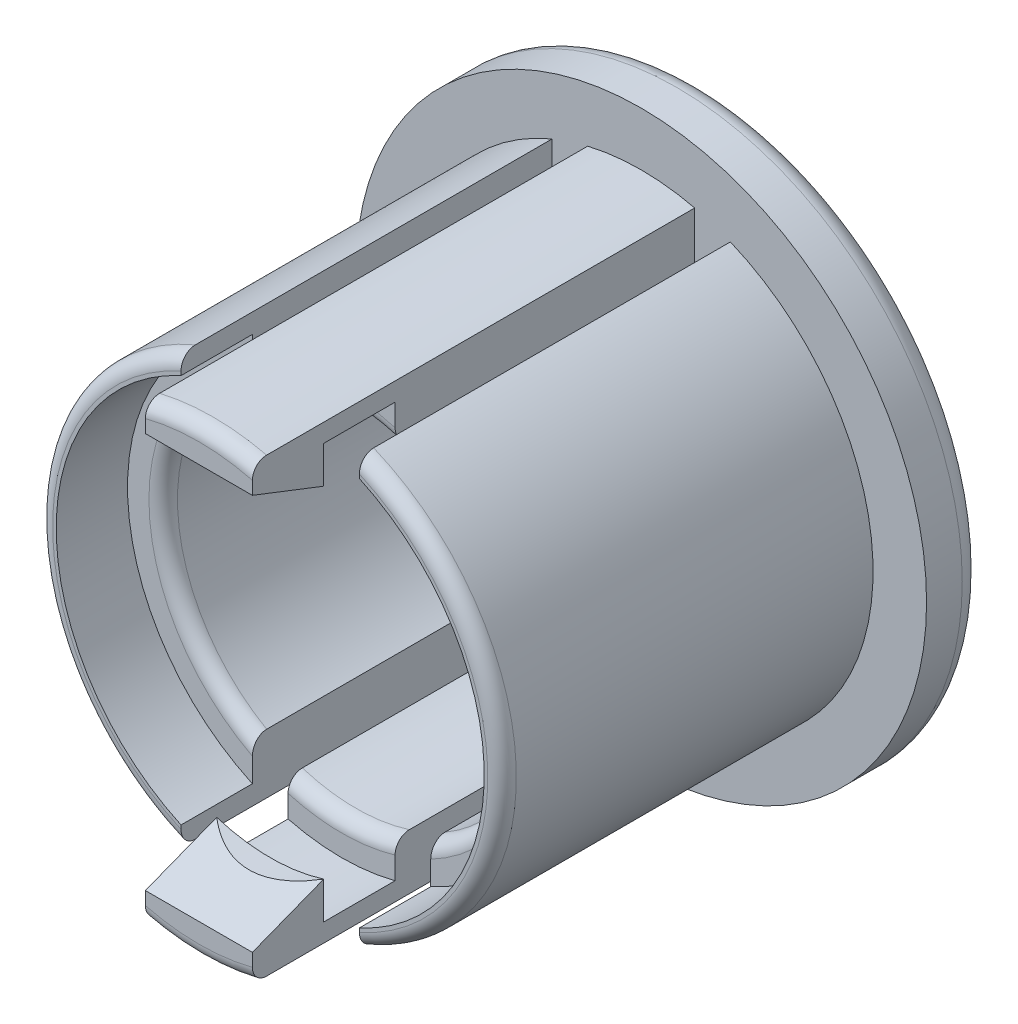
SolidWorks part; units mm, degrees
material "ABS"
ref_plane "Спереди" through (0, 0, 0) normal (0, 0, 1) x (1, 0, 0)
ref_plane "Сверху" through (0, 0, 0) normal (0, 1, 0) x (1, 0, 0)
ref_plane "Справа" through (0, 0, 0) normal (1, 0, 0) x (0, 0, -1)
sketch "Эскиз1" plane through (0, 0, 0) normal (0, 0, 1) x (1, 0, 0)
  circle A0 centre (0, 0) radius 4
  dimension "D1" = 8
extrude "Бобышка-Вытянуть1" add sketch "Эскиз1" along normal blind 0.8
sketch "Эскиз2" plane through (0, 0, 0.8) normal (0, 0, 1) x (1, 0, 0)
  circle A0 centre (0, 0) radius 3.25
  dimension "D1" = 6.5
extrude "Бобышка-Вытянуть2" add sketch "Эскиз2" along normal blind 6.2
sketch "Эскиз3" plane through (0, 0, 7) normal (0, 0, 1) x (1, 0, 0)
  circle A0 centre (0, 0) radius 2.5
  dimension "D1" = 5
extrude "Вырез-Вытянуть1" cut sketch "Эскиз3" against normal through all both and the other way through all
sketch "Эскиз4" plane through (0, 0, 7) normal (0, 0, 1) x (1, 0, 0)
  line L1 (-1.25, 4) -> (-0.75, 4)
  line L2 (-1.25, 4) -> (-1.25, -4)
  line L3 (-1.25, -4) -> (-0.75, -4)
  line L4 (-0.75, 4) -> (-0.75, -4)
  line L5 (1.25, 4) -> (0.75, 4)
  line L6 (1.25, 4) -> (1.25, -4)
  line L7 (1.25, -4) -> (0.75, -4)
  line L8 (0.75, 4) -> (0.75, -4)
  dimension "D1" = 0.5
  dimension "D2" = 8
  dimension "D3" = 0.75
  dimension "D4" = 4
  dimension "D5" = 0.5
  dimension "D6" = 0.75
extrude "Вырез-Вытянуть2" cut sketch "Эскиз4" against normal blind 6.2
sketch "Эскиз5" plane through (0, 0, 7) normal (0, 0, 1) x (1, 0, 0)
  line L1 (-1.25, 3) -> (-3.25, 3)
  line L2 (-1.25, 3) -> (-1.25, -3)
  line L3 (-1.25, -3) -> (-3.25, -3)
  line L4 (-3.25, 3) -> (-3.25, -3)
  line L5 (1.25, 3) -> (3.25, 3)
  line L6 (1.25, 3) -> (1.25, -3)
  line L7 (1.25, -3) -> (3.25, -3)
  line L8 (3.25, 3) -> (3.25, -3)
  dimension "D1" = 6
  dimension "D2" = 2
  dimension "D3" = 2
  dimension "D4" = 6
extrude "Вырез-Вытянуть3" cut sketch "Эскиз5" against normal blind 1
sketch "Эскиз6" plane through (0, 0, 6) normal (0, 0, 1) x (1, 0, 0)
  circle A0 centre (0, 0) radius 3
  dimension "D1" = 6
extrude "Вырез-Вытянуть4" cut sketch "Эскиз6" against normal blind 1
sketch "Эскиз7" plane through (-0.75, 0, 0) normal (-1, 0, 0) x (0, 0, 1)
  line L0 (7, 2.7736) -> (6, 2.3848)
  line L1 (7, 2.3848) -> (7, 3.1623) construction
  line L2 (6, 2.3848) -> (7, 2.3848)
  line L3 (7, 2.3848) -> (7, 2.7736)
  line L4 (7, -2.7736) -> (6, -2.3848)
  line L5 (7, -3.1623) -> (7, -2.3848) construction
  line L6 (6, -2.3848) -> (7, -2.3848)
  line L7 (7, -2.3848) -> (7, -2.7736)
extrude "Вырез-Вытянуть5" cut sketch "Эскиз7" against normal through all
fillet "Скругление1" radius 0.3 2 edges at (4, 0, 0) (2.5, 0, 0)
fillet "Скругление2" radius 0.2 8 edges at (2.5, 0, 5) (0, -2.5, 5) (0, 2.5, 5) (-2.5, 0, 5) (0, 3.25, 7) (0, -3.25, 7) (3.25, 0, 6) (-3.25, 0, 6)
